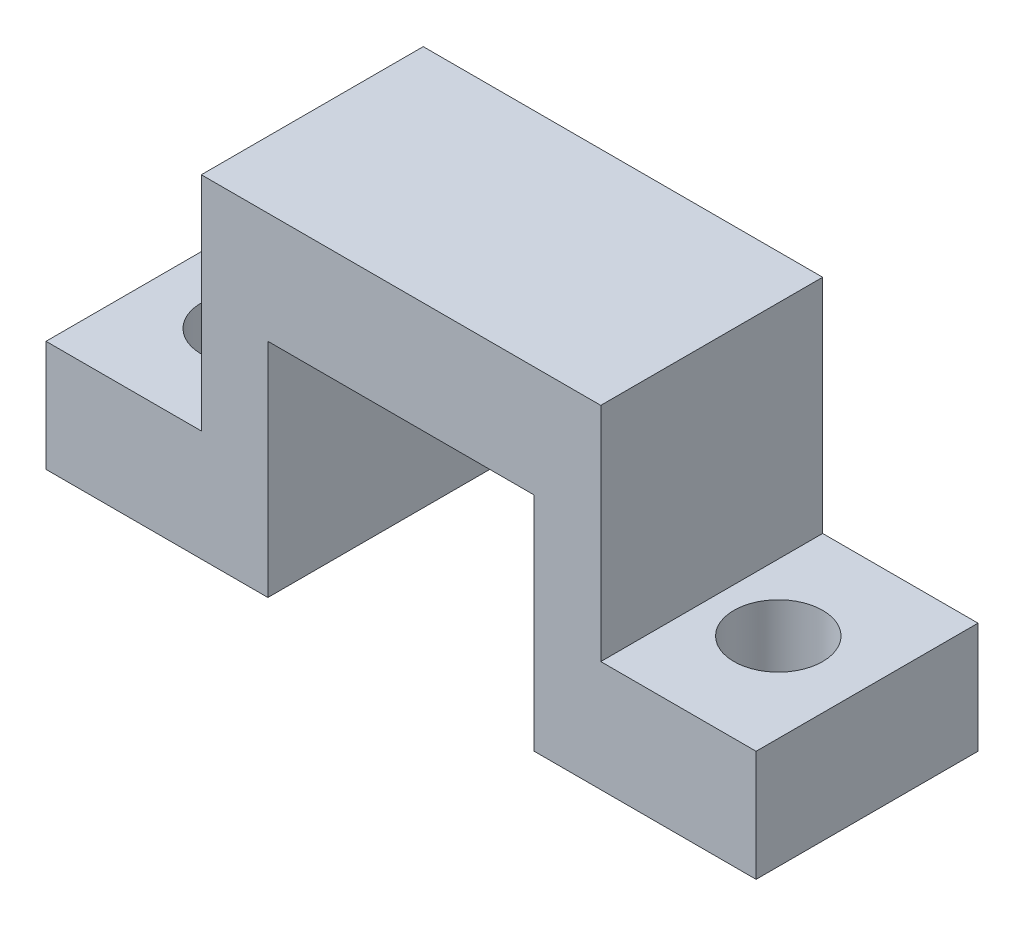
SolidWorks part; units mm, degrees
ref_plane "Plano frontal" through (0, 0, 0) normal (0, 0, 1) x (1, 0, 0)
ref_plane "Plano superior" through (0, 0, 0) normal (0, 1, 0) x (1, 0, 0)
ref_plane "Plano direito" through (0, 0, 0) normal (1, 0, 0) x (0, 0, -1)
sketch "Esboço1" plane through (0, 0, 0) normal (0, 0, 1) x (1, 0, 0)
  line L5 (32, 0) -> (32, 15)
  line L6 (32, 15) -> (0, 15)
  line L7 (0, 15) -> (0, 0)
  line L8 (16, 15) -> (16, 0) construction
  line L9 (10, 10) -> (22, 10)
  line L10 (22, 10) -> (22, 0)
  line L11 (22, 0) -> (32, 0)
  line L12 (10, 0) -> (0, 0)
  line L13 (10, 10) -> (10, 0)
  point P12 (16, 10)
  dimension "D1" = 32
  dimension "D2" = 6
  dimension "D3" = 10
  dimension "D4" = 15
  dimension "D5" = 10
extrude "Ressalto-extrusão1" add sketch "Esboço1" along normal blind 10
sketch "Esboço2" plane through (0, 0, 0) normal (0, -1, 0) x (-1, 0, 0)
  line L0 (0, -5) -> (-32, -5) construction
  line L1 (0, -10) -> (0, 0) construction
  line L2 (-32, -10) -> (-32, 0) construction
  circle A0 centre (-4, -5) radius 2
  circle A1 centre (-28, -5) radius 2
  dimension "D1" = 4
  dimension "D2" = 4
  dimension "D3" = 4
  dimension "D4" = 4
extrude "Corte-extrusão1" cut sketch "Esboço2" against normal blind 20
sketch "Esboço4" plane through (0, 0, 0) normal (0, 0, -1) x (-1, 0, 0)
  line L1 (-32, 15) -> (-25, 15)
  line L2 (-32, 15) -> (-32, 5)
  line L3 (-32, 5) -> (-25, 5)
  line L4 (-25, 15) -> (-25, 5)
  line L5 (0, 15) -> (-7, 15)
  line L6 (0, 15) -> (0, 5)
  line L7 (0, 5) -> (-7, 5)
  line L8 (-7, 15) -> (-7, 5)
  dimension "D1" = 10
  dimension "D2" = 7
  dimension "D3" = 10
  dimension "D4" = 7
extrude "Corte-extrusão2" cut sketch "Esboço4" against normal blind 20
